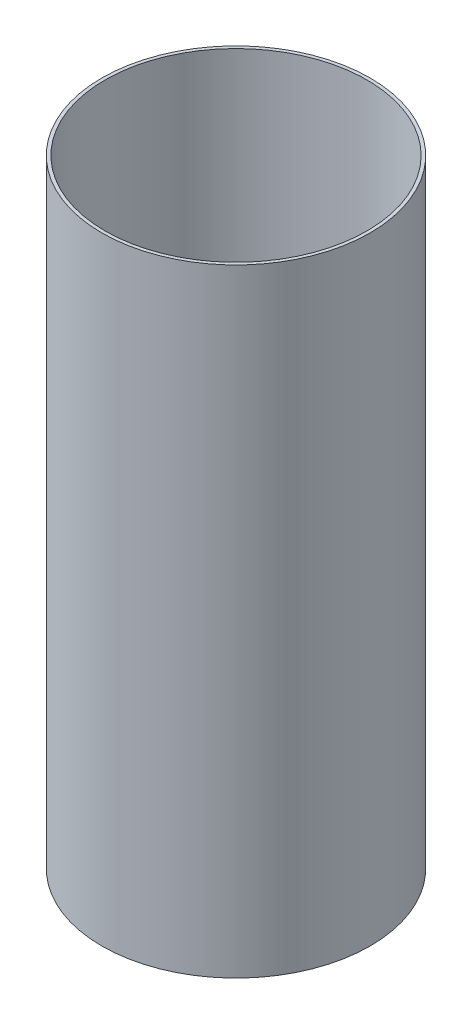
SolidWorks part; units mm, degrees
material "6061-T6 (SS)"
ref_plane "Front Plane" through (0, 0, 0) normal (0, 0, 1) x (1, 0, 0)
ref_plane "Top Plane" through (0, 0, 0) normal (0, 1, 0) x (1, 0, 0)
ref_plane "Right Plane" through (0, 0, 0) normal (1, 0, 0) x (0, 0, -1)
sketch "Sketch1" plane through (0, 0, 0) normal (0, 1, 0) x (1, 0, 0)
  circle A0 centre (0, 0) radius 76.55
  circle A1 centre (0, 0) radius 82.55
  dimension "D1" = 165.1
  dimension "D2" = 6
extrude "Boss-Extrude1" add sketch "Sketch1" along normal blind 380
sketch "Sketch2" plane through (0, 0, 0) normal (0, -1, 0) x (1, 0, 0)
  circle A0 centre (0, 0) radius 80.55
  dimension "D1" = 161.1
extrude "Cut-Extrude1" cut sketch "Sketch2" against normal blind 170
sketch "Sketch3" plane through (0, 380, 0) normal (0, 1, 0) x (1, 0, 0)
  circle A0 centre (0, 0) radius 80.55
  dimension "D1" = 161.1
extrude "Cut-Extrude2" cut sketch "Sketch3" against normal blind 155
equation "\"TubeDiameter\" = 6.500in"
equation "\"D1@Sketch1\"=\"TubeDiameter\""
